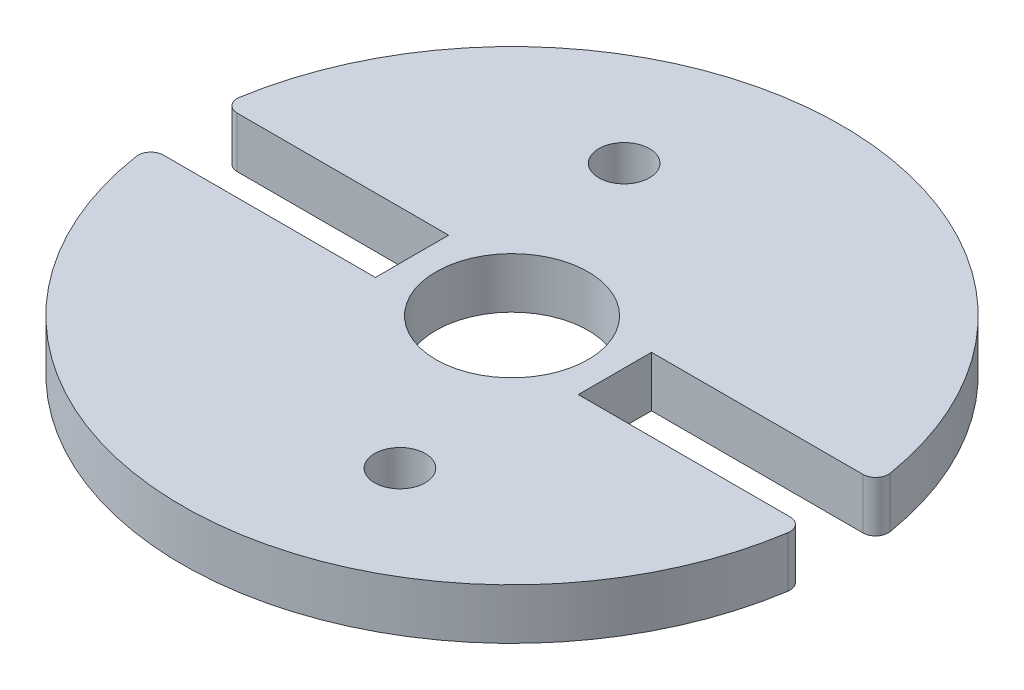
SolidWorks part; units mm, degrees
ref_plane "Front Plane" through (0, 0, 0) normal (0, 0, 1) x (1, 0, 0)
ref_plane "Top Plane" through (0, 0, 0) normal (0, 1, 0) x (1, 0, 0)
ref_plane "Right Plane" through (0, 0, 0) normal (1, 0, 0) x (0, 0, -1)
sketch "Sketch1" plane through (0, 0, 0) normal (0, 1, 0) x (1, 0, 0)
  line L0 (-12.339, 1.5) -> (-4, 1.5)
  line L1 (-12.3566, -1.388) -> (-4, -1.388)
  line L2 (-4, 1.5) -> (-4, -1.388)
  line L3 (0, 16.3908) -> (0, -22.5927) construction
  line L4 (4, 1.5) -> (4, -1.388)
  line L5 (12.3566, -1.388) -> (4, -1.388)
  line L6 (12.339, 1.5) -> (4, 1.5)
  line L7 (-5.7454, 14.2204) -> (0, 0) construction
  line L8 (0, 0) -> (-18.8171, -7.6026) construction
  arc A0 (-12.8509, -1.9636) -> (12.8509, -1.9636) centre (0, 0) ccw
  arc A1 (-12.8509, -1.9636) -> (-12.3566, -1.388) centre (-12.3566, -1.888) cw
  arc A2 (-12.8325, 2.08) -> (-12.339, 1.5) centre (-12.339, 2) ccw
  arc A3 (12.8325, 2.08) -> (-12.8325, 2.08) centre (0, 0) ccw
  arc A4 (12.8509, -1.9636) -> (12.3566, -1.388) centre (12.3566, -1.888) ccw
  arc A5 (12.8325, 2.08) -> (12.339, 1.5) centre (12.339, 2) cw
  circle A6 centre (-2.9969, 7.4175) radius 1
  circle A7 centre (2.9969, -7.4175) radius 1
  circle A8 centre (0, 0) radius 3
  point P14 (-12.9257, -1.388)
  point P17 (-12.9132, 1.5)
  point P20 (12.9257, -1.388)
  point P23 (12.9132, 1.5)
  dimension "D1" = 26
  dimension "D3" = 0.5
  dimension "D6" = 0.5
  dimension "D7" = 2
  dimension "D2" = 1.5
  dimension "D4" = 4
  dimension "D5" = 4
  dimension "D8" = 22
  dimension "D9" = 8
  dimension "D10" = 90
extrude "Boss-Extrude1" add sketch "Sketch1" along normal blind 2
